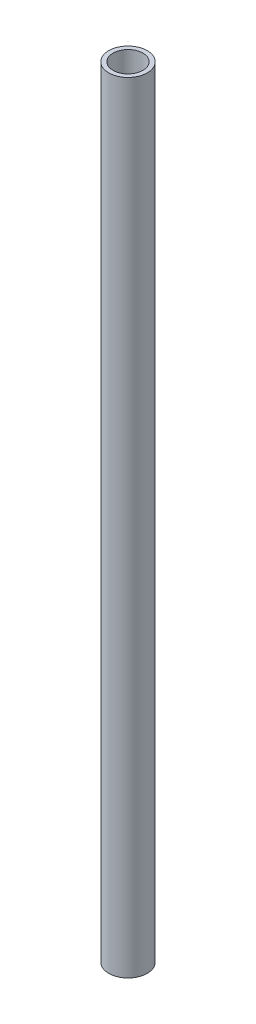
SolidWorks part; units mm, degrees
ref_plane "Front Plane" through (0, 0, 0) normal (0, 0, 1) x (1, 0, 0)
ref_plane "Top Plane" through (0, 0, 0) normal (0, 1, 0) x (1, 0, 0)
ref_plane "Right Plane" through (0, 0, 0) normal (1, 0, 0) x (0, 0, -1)
sketch "Sketch1" plane through (0, 0, 0) normal (0, 1, 0) x (1, 0, 0)
  circle A0 centre (0, 0) radius 57
extrude "Boss-Extrude1" add sketch "Sketch1" along normal blind 2307.62
sketch "Sketch2" plane through (0, 2307.62, 0) normal (0, 1, 0) x (1, 0, 0)
  point P0 (0, 0)
shell "Shell1" thickness 12.7
